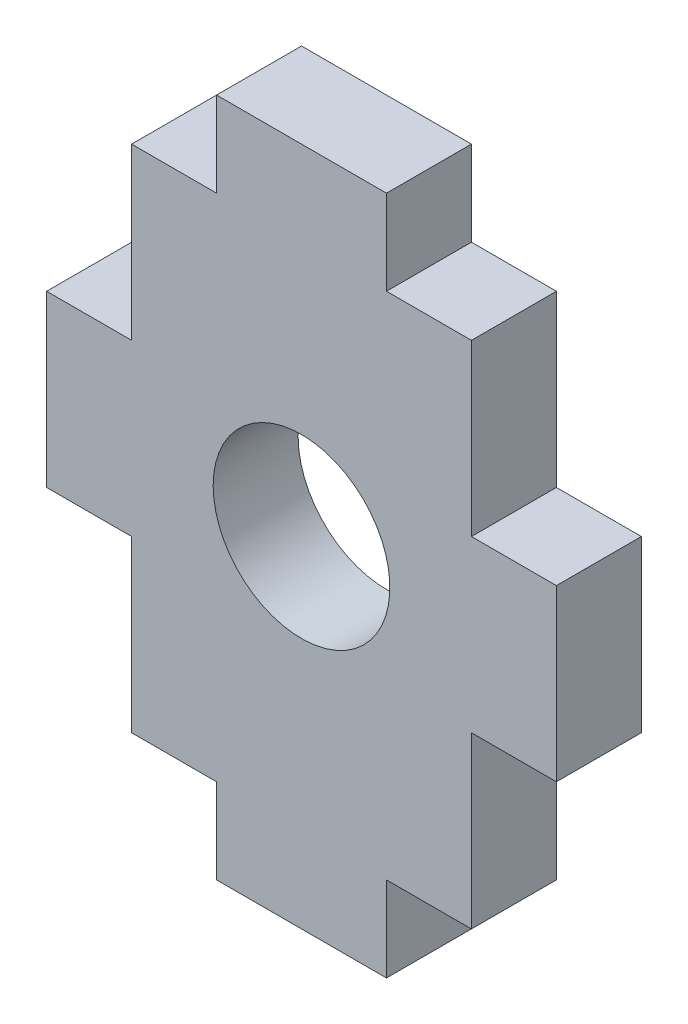
SolidWorks part; units mm, degrees
ref_plane "Front Plane" through (0, 0, 0) normal (0, 0, 1) x (1, 0, 0)
ref_plane "Top Plane" through (0, 0, 0) normal (0, 1, 0) x (1, 0, 0)
ref_plane "Right Plane" through (0, 0, 0) normal (1, 0, 0) x (0, 0, -1)
sketch "Sketch1" plane through (0, 0, 0) normal (0, 0, 1) x (1, 0, 0)
  line L0 (0, -12.7) -> (0, 12.7) construction
  line L1 (3.175, 9.525) -> (6.35, 9.525)
  line L2 (-6.35, 9.525) -> (-6.35, 3.175)
  line L3 (0, 0) -> (35.3222, 0) construction
  line L4 (9.525, 3.175) -> (9.525, -3.175)
  line L5 (6.35, 3.175) -> (9.525, 3.175)
  line L6 (3.175, 12.7) -> (3.175, 9.525)
  line L7 (-3.175, 12.7) -> (3.175, 12.7)
  line L8 (-3.175, 12.7) -> (-3.175, 9.525)
  line L9 (6.35, 9.525) -> (6.35, 3.175)
  line L10 (3.175, -9.525) -> (6.35, -9.525)
  line L11 (-6.35, 3.175) -> (-9.525, 3.175)
  line L12 (-6.35, -3.175) -> (-9.525, -3.175)
  line L13 (-6.35, 9.525) -> (-3.175, 9.525)
  line L14 (-9.525, 3.175) -> (-9.525, -3.175)
  line L15 (6.35, -9.525) -> (6.35, -3.175)
  line L16 (-3.175, -12.7) -> (-3.175, -9.525)
  line L17 (-3.175, -12.7) -> (3.175, -12.7)
  line L18 (3.175, -12.7) -> (3.175, -9.525)
  line L19 (6.35, -3.175) -> (9.525, -3.175)
  line L20 (-6.35, -9.525) -> (-6.35, -3.175)
  line L21 (-6.35, -9.525) -> (-3.175, -9.525)
  point P18 (-9.525, 0)
  point P26 (9.525, 0)
  dimension "D2" = 3.175
  dimension "D3" = 3.175
  dimension "D4" = 25.4
  dimension "D5" = 3.175
  dimension "D6" = 3.175
extrude "Extrude1" add sketch "Sketch1" along normal blind 3.175
sketch "Sketch2" plane through (0, 0, 0) normal (0, 0, -1) x (-1, 0, 0)
  circle A0 centre (0, 0) radius 3.302
  dimension "D1" = 6.604
extrude "Cut-Extrude1" cut sketch "Sketch2" against normal blind 3.175
